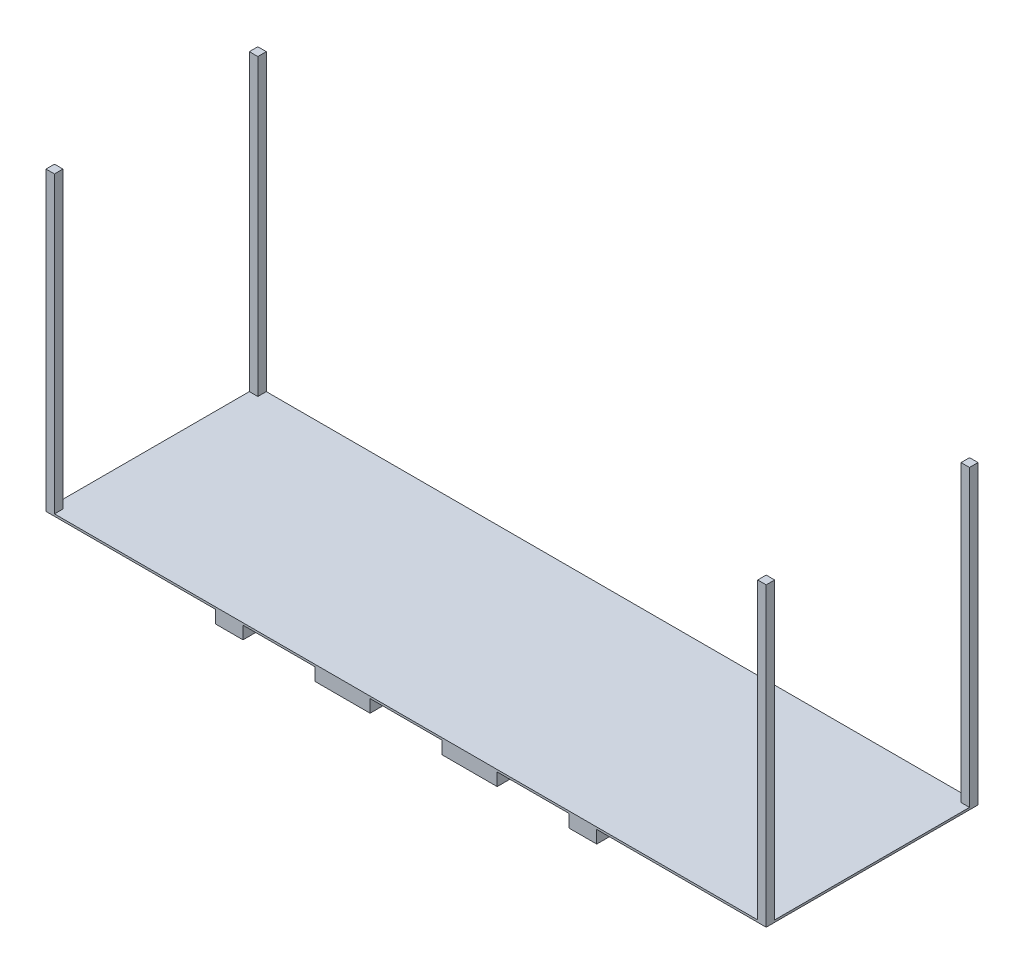
SolidWorks part; units mm, degrees
ref_plane "Front Plane" through (0, 0, 0) normal (0, 0, 1) x (1, 0, 0)
ref_plane "Top Plane" through (0, 0, 0) normal (0, 1, 0) x (1, 0, 0)
ref_plane "Right Plane" through (0, 0, 0) normal (1, 0, 0) x (0, 0, -1)
sketch "Sketch1" plane through (0, 0, 0) normal (0, 1, 0) x (1, 0, 0)
  line L1 (0, 0) -> (1700, 0)
  line L2 (0, 0) -> (0, 500)
  line L3 (0, 500) -> (1700, 500)
  line L4 (1700, 0) -> (1700, 500)
  dimension "D1" = 1700
  dimension "D2" = 500
extrude "Boss-Extrude1" add sketch "Sketch1" along normal blind 5
sketch "Sketch2" plane through (0, 5, 0) normal (0, 1, 0) x (1, 0, 0)
  line L0 (850, 616.6334) -> (850, -325.496) construction
  line L1 (0, 500) -> (20, 500)
  line L2 (0, 500) -> (0, 480)
  line L3 (0, 480) -> (20, 480)
  line L4 (20, 500) -> (20, 480)
  line L7 (20, 0) -> (20, 20)
  line L8 (0, 20) -> (20, 20)
  line L9 (0, 0) -> (0, 20)
  line L10 (0, 0) -> (20, 0)
  line L11 (1700, 0) -> (1680, 0)
  line L12 (1700, 0) -> (1700, 20)
  line L13 (1700, 20) -> (1680, 20)
  line L14 (1680, 0) -> (1680, 20)
  line L15 (1680, 500) -> (1680, 480)
  line L16 (1700, 480) -> (1680, 480)
  line L17 (1700, 500) -> (1700, 480)
  line L18 (1700, 500) -> (1680, 500)
  dimension "D1" = 20
  dimension "D2" = 20
extrude "Boss-Extrude2" add sketch "Sketch2" along normal blind 695
sketch "Sketch3" plane through (0, 0, 0) normal (0, -1, 0) x (1, 0, 0)
  line L0 (1700, -500) -> (0, -500) construction
  line L1 (400, -500) -> (1300, -500)
  line L2 (400, -500) -> (400, 0)
  line L3 (400, 0) -> (1300, 0)
  line L4 (1300, -500) -> (1300, 0)
  line L5 (0, 0) -> (1700, 0) construction
  line L6 (0, -500) -> (0, 0) construction
  line L7 (1700, 0) -> (1700, -500) construction
  dimension "D1" = 400
  dimension "D2" = 400
extrude "Boss-Extrude3" add sketch "Sketch3" along normal blind 30
sketch "Sketch4" plane through (0, -30, 0) normal (0, -1, 0) x (1, 0, 0)
  line L0 (1300, 0) -> (400, 0) construction
  line L1 (465, 0) -> (635, 0)
  line L2 (465, 0) -> (465, -500)
  line L3 (465, -500) -> (635, -500)
  line L4 (635, 0) -> (635, -500)
  line L5 (400, -500) -> (1300, -500) construction
  line L6 (400, 0) -> (400, -500) construction
  line L8 (765, -500) -> (935, -500)
  line L9 (765, -500) -> (765, 0)
  line L10 (765, 0) -> (935, 0)
  line L11 (935, -500) -> (935, 0)
  line L12 (1065, -500) -> (1235, -500)
  line L13 (1065, -500) -> (1065, 0)
  line L14 (1065, 0) -> (1235, 0)
  line L15 (1235, -500) -> (1235, 0)
  dimension "D1" = 65
  dimension "D2" = 170
  dimension "D3" = 170
  dimension "D4" = 130
  dimension "D5" = 170
  dimension "D6" = 130
extrude "Cut-Extrude1" cut sketch "Sketch4" against normal blind 30
